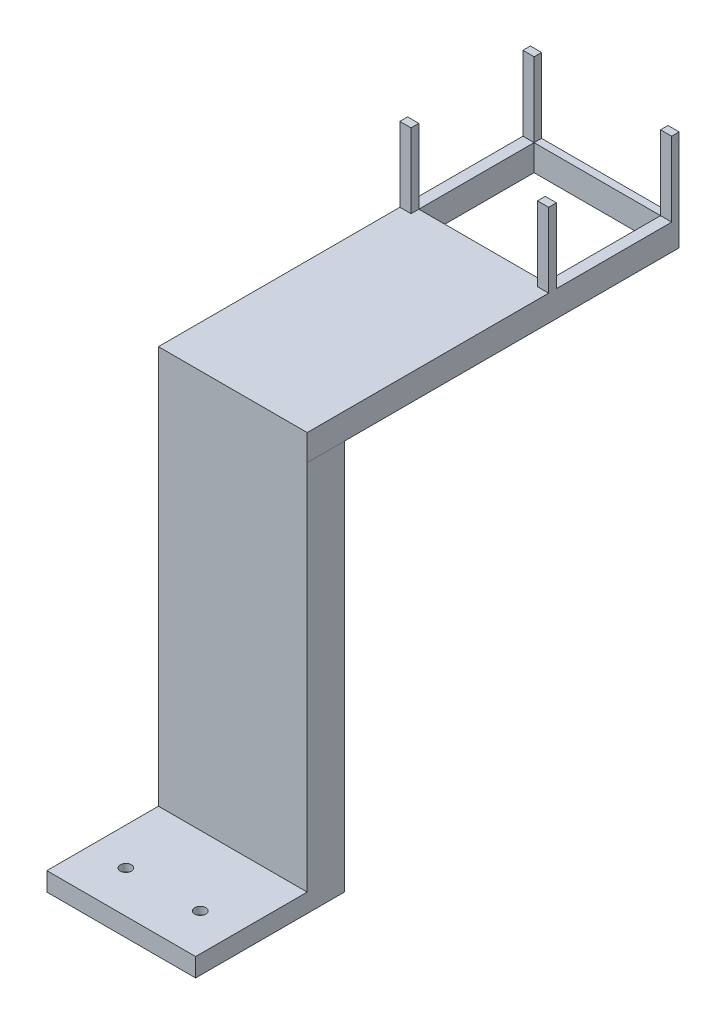
SolidWorks part; units mm, degrees
ref_plane "Front Plane" through (0, 0, 0) normal (0, 0, 1) x (1, 0, 0)
ref_plane "Top Plane" through (0, 0, 0) normal (0, 1, 0) x (1, 0, 0)
ref_plane "Right Plane" through (0, 0, 0) normal (1, 0, 0) x (0, 0, -1)
sketch "Sketch1" plane through (0, 0, 0) normal (0, 1, 0) x (1, 0, 0)
  line L1 (0, 0) -> (40, 0)
  line L2 (0, 0) -> (0, 40)
  line L3 (0, 40) -> (40, 40)
  line L4 (40, 0) -> (40, 40)
  dimension "D1" = 40
  dimension "D2" = 40
extrude "Boss-Extrude1" add sketch "Sketch1" along normal blind 5
sketch "Sketch2" plane through (0, 5, 0) normal (0, 1, 0) x (1, 0, 0)
  line L0 (40, 0) -> (40, 40) construction
  line L1 (0, 40) -> (40, 40)
  line L2 (0, 40) -> (0, 28)
  line L3 (0, 28) -> (40, 28)
  line L4 (40, 40) -> (40, 28)
  line L5 (0, 28) -> (0, 0) construction
  line L6 (0, 0) -> (0, 14) construction
  line L7 (0, 14) -> (40, 14) construction
  line L8 (40, 14) -> (20, 8.5035) construction
  line L9 (20, 8.5035) -> (0, 14) construction
  circle A0 centre (10, 11.2517) radius 1.5
  circle A1 centre (30, 11.2517) radius 1.5
  dimension "D2" = 3
  dimension "D1" = 12
extrude "Cut-Extrude1" cut sketch "Sketch2" against normal blind 2 contours A0 | A1
sketch "Sketch5" plane through (0, 5, 0) normal (0, 1, 0) x (1, 0, 0)
  line L0 (40, 0) -> (40, 40) construction
  line L1 (0, 40) -> (40, 40)
  line L2 (0, 40) -> (0, 30)
  line L3 (0, 30) -> (40, 30)
  line L4 (40, 40) -> (40, 30)
  dimension "D1" = 10
extrude "Boss-Extrude2" add sketch "Sketch5" along normal blind 100
sketch "Sketch6" plane through (0, 105, 0) normal (0, 1, 0) x (1, 0, 0)
  line L1 (0, 30) -> (40.0034, 30)
  line L2 (0, 30) -> (0, 130)
  line L3 (0, 130) -> (40.0034, 130)
  line L4 (40.0034, 30) -> (40.0034, 130)
  dimension "D1" = 100
extrude "Boss-Extrude3" add sketch "Sketch6" along normal blind 7
sketch "Sketch7" plane through (0, 112, 0) normal (0, 1, 0) x (1, 0, 0)
  line L0 (3.0017, 112.5) -> (0, 112.5) construction
  line L1 (3.0017, 128) -> (37.0017, 128)
  line L2 (3.0017, 128) -> (3.0017, 97)
  line L3 (3.0017, 97) -> (37.0017, 97)
  line L4 (37.0017, 128) -> (37.0017, 97)
  line L5 (0, 130) -> (0, 30) construction
  line L6 (37.0017, 112.5) -> (40.0034, 112.5) construction
  line L7 (40.0034, 30) -> (40.0034, 130) construction
  line L8 (20.0017, 128) -> (20.0017, 130) construction
  line L9 (40.0034, 130) -> (0, 130) construction
  dimension "D1" = 34
  dimension "D2" = 2
  dimension "D3" = 31
extrude "Cut-Extrude2" cut sketch "Sketch7" against normal blind 100
sketch "Sketch8" plane through (0, 112, 0) normal (0, 1, 0) x (1, 0, 0)
  line L0 (0, 130) -> (0, 30) construction
  line L1 (37.0017, 128) -> (40.0034, 128)
  line L2 (37.0017, 128) -> (37.0017, 130)
  line L3 (37.0017, 130) -> (40.0034, 130)
  line L4 (40.0034, 128) -> (40.0034, 130)
  line L5 (3.0017, 128) -> (0, 128)
  line L6 (3.0017, 128) -> (3.0017, 130)
  line L7 (3.0017, 130) -> (0, 130)
  line L8 (0, 128) -> (0, 130)
  line L9 (3.0017, 97) -> (0, 97)
  line L10 (3.0017, 97) -> (3.0017, 94.9068)
  line L11 (3.0017, 94.9068) -> (0, 94.9068)
  line L12 (0, 97) -> (0, 94.9068)
  line L13 (40.0034, 30) -> (40.0034, 130) construction
  line L14 (37.0017, 97) -> (40.0034, 97)
  line L15 (37.0017, 97) -> (37.0017, 94.9068)
  line L16 (37.0017, 94.9068) -> (40.0034, 94.9068)
  line L17 (40.0034, 97) -> (40.0034, 94.9068)
extrude "Boss-Extrude4" add sketch "Sketch8" along normal blind 20
